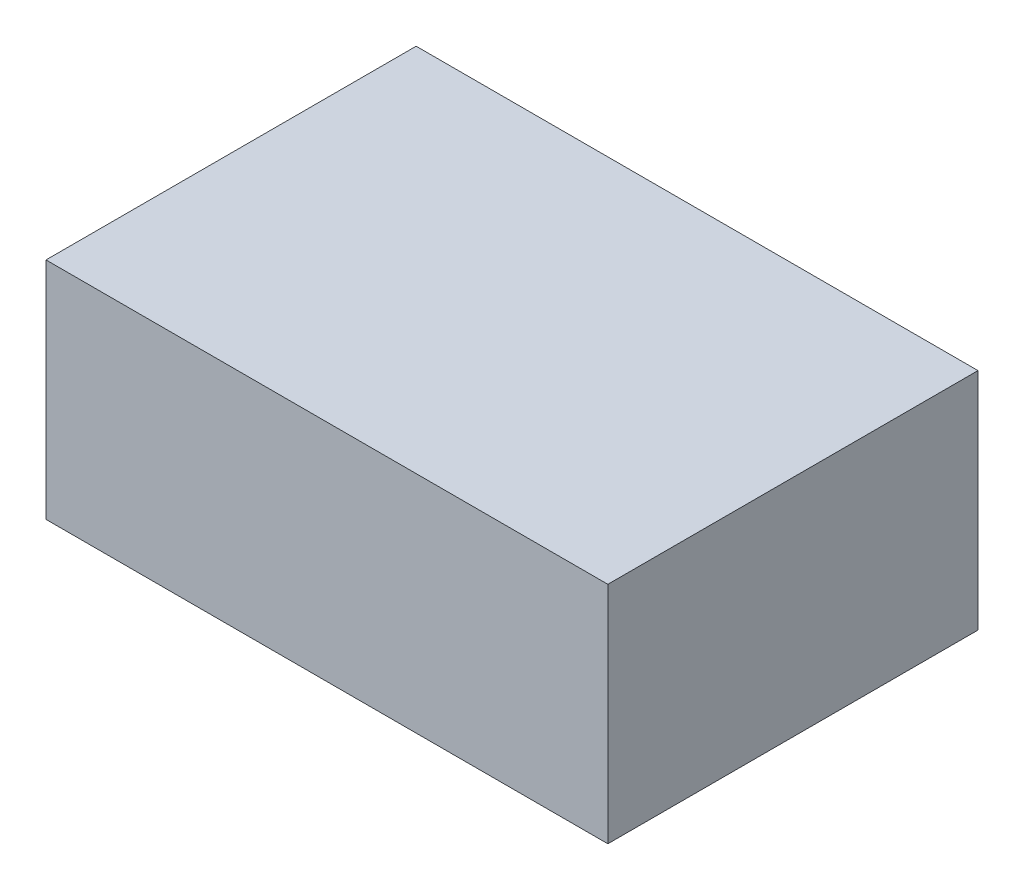
SolidWorks part; units mm, degrees
ref_plane "Płaszczyzna przednia" through (0, 0, 0) normal (0, 0, 1) x (1, 0, 0)
ref_plane "Płaszczyzna górna" through (0, 0, 0) normal (0, 1, 0) x (1, 0, 0)
ref_plane "Płaszczyzna prawa" through (0, 0, 0) normal (1, 0, 0) x (0, 0, -1)
sketch "Sketch1" plane through (0, 0, 0) normal (0, 1, 0) x (1, 0, 0)
  line L1 (-42.5, -28) -> (42.5, -28)
  line L2 (-42.5, -28) -> (-42.5, 28)
  line L3 (-42.5, 28) -> (42.5, 28)
  line L4 (42.5, -28) -> (42.5, 28)
  line L5 (-42.5, -28) -> (42.5, 28) construction
  line L6 (-42.5, 28) -> (42.5, -28) construction
  point P0 (0, 0)
  dimension "D1" = 85
  dimension "D2" = 56
extrude "Boss-Extrude1" add sketch "Sketch1" along normal blind 34
